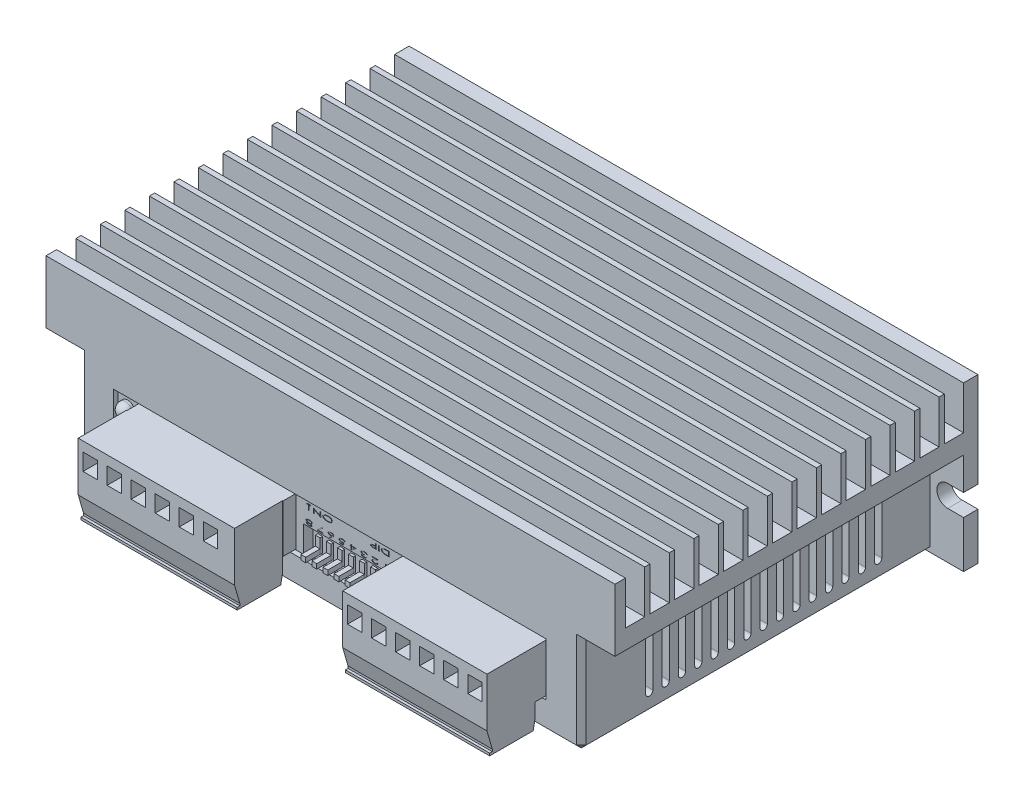
SolidWorks part; units mm, degrees
ref_plane "Ebene vorne" through (0, 0, 0) normal (0, 0, 1) x (1, 0, 0)
ref_plane "Ebene oben" through (0, 0, 0) normal (0, 1, 0) x (1, 0, 0)
ref_plane "Ebene rechts" through (0, 0, 0) normal (1, 0, 0) x (0, 0, -1)
sketch "Skizze1" plane through (0, 0, 0) normal (0, 0, 1) x (1, 0, 0)
  line L1 (-50.054, 15.2488) -> (68.246, 15.2488)
  line L2 (-50.054, 15.2488) -> (-50.054, -18.7512)
  line L3 (-50.054, -18.7512) -> (68.246, -18.7512)
  line L4 (68.246, 15.2488) -> (68.246, -18.7512)
  dimension "D1" = 118.3
  dimension "D2" = 34
extrude "Grundkörper" add sketch "Skizze1" along normal blind 75.5
sketch "Skizze2" plane through (0, 0, 75.5) normal (0, 0, 1) x (1, 0, 0)
  line L0 (-50.054, 15.2488) -> (-50.054, -18.7512) construction
  line L1 (-50.054, -18.7512) -> (68.246, -18.7512) construction
  line L2 (-47.054, -9.0012) -> (-50.054, -9.0012)
  line L3 (-50.054, -9.0012) -> (-50.054, -4.5012)
  line L4 (-50.054, -4.5012) -> (-47.054, -4.5012)
  line L5 (64.946, -4.5012) -> (68.246, -4.5012)
  line L6 (68.246, -4.5012) -> (68.246, -9.0012)
  line L7 (68.246, -9.0012) -> (64.946, -9.0012)
  arc A0 (-47.054, -9.0012) -> (-47.054, -4.5012) centre (-47.054, -6.7512) ccw
  arc A1 (64.946, -4.5012) -> (64.946, -9.0012) centre (64.946, -6.7512) ccw
  dimension "D2" = 4.5
  dimension "D3" = 112
  dimension "D4" = 3
  dimension "D5" = 12
  dimension "D6" = 12
  dimension "D8" = 2.25
extrude "Befestigung" cut sketch "Skizze2" against normal through all
sketch "Skizze3" plane through (0, 0, 75.5) normal (0, 0, 1) x (1, 0, 0)
  line L0 (68.246, -4.5012) -> (68.246, 15.2488) construction
  line L1 (-50.054, 2.2488) -> (-43.054, 2.2488)
  line L2 (-50.054, 2.2488) -> (-50.054, -18.7512)
  line L3 (-50.054, -18.7512) -> (-43.054, -18.7512)
  line L4 (-43.054, 2.2488) -> (-43.054, -18.7512)
  line L5 (68.246, 2.2488) -> (61.246, 2.2488)
  line L6 (68.246, 2.2488) -> (68.246, -18.7512)
  line L7 (68.246, -18.7512) -> (61.246, -18.7512)
  line L8 (61.246, 2.2488) -> (61.246, -18.7512)
  line L9 (-50.054, -18.7512) -> (68.246, -18.7512) construction
  dimension "D1" = 7
  dimension "D2" = 7
  dimension "D3" = 0
  dimension "D4" = 21
  dimension "D5" = 21
  dimension "D6" = 0
extrude "Seitentaschen" cut sketch "Skizze3" against normal blind 72.5
sketch "Skizze4" plane through (0, 15.2488, 0) normal (0, 1, 0) x (1, 0, 0)
  line L0 (68.246, 0) -> (-50.054, 0) construction
  line L1 (-50.054, -3) -> (68.246, -3)
  line L2 (-50.054, -3) -> (-50.054, -7)
  line L3 (-50.054, -7) -> (68.246, -7)
  line L4 (68.246, -3) -> (68.246, -7)
  dimension "D1" = 3
  dimension "D2" = 4
extrude "Kühlrippen hinten" cut sketch "Skizze4" against normal blind 9
pattern_linear "Kühlrippen hinten Muster" count 14 spacing 5.1 along (0, 0, 1) of "Kühlrippen hinten"
sketch "Skizze5" plane through (-43.054, 0, 0) normal (-1, 0, 0) x (0, 0, 1)
  line L0 (13.75, -4.7512) -> (13.75, -14.7512) construction
  line L1 (14.5, -4.7512) -> (14.5, -14.7512)
  line L2 (13, -4.7512) -> (13, -14.7512)
  line L3 (3, -9.0012) -> (3, -18.7512) construction
  line L4 (3, -18.7512) -> (75.5, -18.7512) construction
  arc A0 (14.5, -4.7512) -> (13, -4.7512) centre (13.75, -4.7512) ccw
  arc A1 (13, -14.7512) -> (14.5, -14.7512) centre (13.75, -14.7512) ccw
  point P2 (13.75, -9.7512)
  dimension "D3" = 10
  dimension "D1" = 1.5
  dimension "D2" = 10
  dimension "D4" = 4
extrude "Kühlrippen seite" cut sketch "Skizze5" against normal through all
pattern_linear "Kühlrippen seite muster" count 15 spacing 3.4 along (0, 0, 1) of "Kühlrippen seite"
sketch "Skizze6" plane through (0, 0, 75.5) normal (0, 0, 1) x (1, 0, 0)
  line L0 (-43.054, -18.7512) -> (-43.054, 2.2488) construction
  line L1 (-36.054, -12.7512) -> (53.946, -12.7512)
  line L2 (-36.054, -12.7512) -> (-36.054, -1.7512)
  line L3 (-36.054, -1.7512) -> (53.946, -1.7512)
  line L4 (53.946, -12.7512) -> (53.946, -1.7512)
  line L5 (68.246, 15.2488) -> (-50.054, 15.2488) construction
  dimension "D1" = 90
  dimension "D2" = 11
  dimension "D3" = 7
  dimension "D4" = 17
extrude "Tasche" cut sketch "Skizze6" against normal blind 1
sketch "Skizze7" plane through (0, 0, 74.5) normal (0, 0, 1) x (1, 0, 0)
  line L0 (53.946, -1.7512) -> (-36.054, -1.7512) construction
  line L1 (-36.054, -1.7512) -> (-36.054, -12.7512) construction
  circle A0 centre (-34.054, -4.7512) radius 1.5
  circle A1 centre (-34.054, -9.7512) radius 1.5
  dimension "D1" = 3
  dimension "D2" = 3
  dimension "D3" = 5
  dimension "D4" = 3
  dimension "D5" = 2
extrude "Leds" add sketch "Skizze7" along normal blind 2
fillet "Led Grün" radius 1.5 1 edges at (-32.554, -4.7512, 76.5)
fillet "Led Rot" radius 1.5 1 edges at (-32.554, -9.7512, 76.5)
sketch "Skizze8" plane through (0, 0, 74.5) normal (0, 0, 1) x (1, 0, 0)
  line L0 (-36.054, -12.7512) -> (53.946, -12.7512) construction
  line L1 (1.446, -2.2512) -> (23.446, -2.2512)
  line L2 (1.446, -2.2512) -> (1.446, -12.2512)
  line L3 (1.446, -12.2512) -> (23.446, -12.2512)
  line L4 (23.446, -2.2512) -> (23.446, -12.2512)
  dimension "D1" = 22
  dimension "D2" = 10
  dimension "D3" = 0.5
  dimension "D4" = 30.5
extrude "DIP Schalter Fläche" add sketch "Skizze8" along normal blind 0.5
sketch "Skizze9" plane through (0, 0, 75) normal (0, 0, 1) x (1, 0, 0)
  line L0 (23.446, -12.2512) -> (23.446, -2.2512) construction
  line L1 (2.946, -12.2512) -> (21.946, -12.2512)
  line L2 (2.946, -12.2512) -> (2.946, -6.7512)
  line L3 (2.946, -6.7512) -> (21.946, -6.7512)
  line L4 (21.946, -12.2512) -> (21.946, -6.7512)
  line L5 (1.446, -12.2512) -> (23.446, -12.2512) construction
  dimension "D1" = 19
  dimension "D2" = 1.5
  dimension "D3" = 5.5
  dimension "D4" = 0
extrude "DIP Schalter Vertiefung" cut sketch "Skizze9" against normal blind 2
sketch "Skizze10" plane through (0, 0, 73) normal (0, 0, 1) x (1, 0, 0)
  line L0 (2.946, -6.7512) -> (2.946, -12.2512) construction
  line L1 (3.946, -9.0512) -> (4.946, -9.0512)
  line L2 (3.946, -9.0512) -> (3.946, -12.0512)
  line L3 (3.946, -12.0512) -> (4.946, -12.0512)
  line L4 (4.946, -9.0512) -> (4.946, -12.0512)
  line L5 (2.946, -12.2512) -> (21.946, -12.2512) construction
  dimension "D1" = 1
  dimension "D2" = 3
  dimension "D3" = 1
  dimension "D4" = 0.2
extrude "DIP Schalter Schalter boden" add sketch "Skizze10" along normal blind 0.5
pattern_linear "DIP Schalter Schalter boden muster" count 8 spacing 2.3 along (1, 0, 0) of "DIP Schalter Schalter boden"
sketch "Skizze11" plane through (0, 0, 74.5) normal (0, 0, 1) x (1, 0, 0)
  line L1 (4.9426, -12.0512) -> (3.9426, -12.0512)
  line L2 (4.9426, -12.0512) -> (4.9426, -11.0512)
  line L3 (4.9426, -11.0512) -> (3.9426, -11.0512)
  line L4 (3.9426, -12.0512) -> (3.9426, -11.0512)
  dimension "D1" = 1
  dimension "D2" = 1
extrude "DIP Schalter Hebel" add sketch "Skizze11" along normal blind 3 from offset 1 separate body offset against normal yes
pattern_linear "DIP Schalter Hebel Muster" count 8 spacing 2.3 along (1, 0, 0) of "DIP Schalter Hebel"
sketch "Skizze12" plane through (0, 0, 75) normal (0, 0, 1) x (1, 0, 0)
  line L0 (3.4242, -5.4773) -> (23.446, -5.4773) construction
  text T0 "1 2 3 4 5 6 7 8\r\nDIP          ON↓" font "Century Gothic" height 1
extrude "DIP Schalter Schrift" cut sketch "Skizze12" against normal blind 0.1
sketch "Skizze14" plane through (0, 0, 74.5) normal (0, 0, 1) x (1, 0, 0)
  line L0 (23.446, -12.2512) -> (23.446, -2.2512) construction
  line L1 (23.646, -2.2512) -> (53.646, -2.2512)
  line L2 (23.646, -2.2512) -> (23.646, -12.2512)
  line L3 (23.646, -12.2512) -> (53.646, -12.2512)
  line L4 (53.646, -2.2512) -> (53.646, -12.2512)
  line L5 (-36.054, -12.7512) -> (53.946, -12.7512) construction
  line L6 (53.946, -1.7512) -> (-36.054, -1.7512) construction
  line L7 (1.246, -2.2512) -> (-31.254, -2.2512)
  line L8 (1.246, -2.2512) -> (1.246, -12.2512)
  line L9 (1.246, -12.2512) -> (-31.254, -12.2512)
  line L10 (-31.254, -2.2512) -> (-31.254, -12.2512)
  line L11 (1.446, -2.2512) -> (1.446, -12.2512) construction
  dimension "D1" = 30
  dimension "D2" = 0.2
  dimension "D3" = 10
  dimension "D4" = 0.5
  dimension "D5" = 32.5
  dimension "D6" = 10
  dimension "D7" = 0.5
  dimension "D8" = 0.2
extrude "Anschlüsse Grund" add sketch "Skizze14" along normal blind 3
sketch "Skizze15" plane through (0, 0, 77.5) normal (0, 0, 1) x (1, 0, 0)
  line L0 (1.246, -2.2512) -> (-31.254, -2.2512) construction
  line L1 (53.646, -2.2512) -> (23.646, -2.2512)
  line L2 (53.646, -2.2512) -> (53.646, -17.2512)
  line L3 (53.646, -17.2512) -> (23.646, -17.2512)
  line L4 (23.646, -2.2512) -> (23.646, -17.2512)
  line L5 (1.1491, -2.2512) -> (-31.3509, -2.2512)
  line L6 (1.1491, -2.2512) -> (1.1491, -17.2512)
  line L7 (1.1491, -17.2512) -> (-31.3509, -17.2512)
  line L8 (-31.3509, -2.2512) -> (-31.3509, -17.2512)
  line L9 (53.646, -2.2512) -> (23.646, -2.2512) construction
  dimension "D1" = 32.5
  dimension "D2" = 30
  dimension "D3" = 15
  dimension "D4" = 0
  dimension "D5" = 15
  dimension "D6" = 0
extrude "Anschlüsse Block" add sketch "Skizze15" along normal blind 10
sketch "Skizze17" plane through (-31.3509, 0, 0) normal (-1, 0, 0) x (0, 0, 1)
  line L0 (87.5, -12.4761) -> (86.3973, -16.3153)
  line L1 (86.3973, -16.3153) -> (86.3973, -16.7527)
  line L2 (86.3973, -16.7527) -> (86.9486, -16.7527)
  line L3 (86.9486, -16.7527) -> (86.9486, -17.2512)
  line L4 (86.9486, -17.2512) -> (87.5, -17.2512)
  line L5 (87.5, -17.2512) -> (87.5, -12.4761)
  line L6 (77.5, -15.2462) -> (77.8927, -17.2512)
  line L7 (77.8927, -17.2512) -> (77.5, -17.2512)
  line L8 (77.5, -17.2512) -> (77.5, -15.2462)
extrude "Anschluss Profil" cut sketch "Skizze17" against normal through all
sketch "Skizze18" plane through (0, 0, 87.5) normal (0, 0, 1) x (1, 0, 0)
  line L1 (-30.3509, -4.2512) -> (-27.3509, -4.2512)
  line L2 (-30.3509, -4.2512) -> (-30.3509, -7.7512)
  line L3 (-30.3509, -7.7512) -> (-27.3509, -7.7512)
  line L4 (-27.3509, -4.2512) -> (-27.3509, -7.7512)
  line L5 (-31.3509, -2.2512) -> (-31.3509, -12.4761) construction
  line L6 (1.246, -2.2512) -> (-31.254, -2.2512) construction
  line L7 (23.646, -2.2512) -> (23.646, -12.4761) construction
  line L8 (24.646, -4.2512) -> (27.646, -4.2512)
  line L9 (24.646, -4.2512) -> (24.646, -7.7512)
  line L10 (24.646, -7.7512) -> (27.646, -7.7512)
  line L11 (27.646, -4.2512) -> (27.646, -7.7512)
  line L12 (53.646, -2.2512) -> (23.646, -2.2512) construction
  dimension "D1" = 3
  dimension "D2" = 3.5
  dimension "D3" = 1
  dimension "D4" = 2
  dimension "D5" = 3
  dimension "D6" = 3.5
  dimension "D7" = 1
  dimension "D8" = 2
extrude "Anschluss Kabel" cut sketch "Skizze18" against normal blind 5
pattern_linear "Anschluss Kabel Muster" count 6 spacing 5 along (1, 0, 0) of "Anschluss Kabel"
sketch "Skizze19" plane through (0, -17.2512, 0) normal (0, -1, 0) x (1, 0, 0)
  line L0 (1.1491, 77.8927) -> (-31.3509, 77.8927) construction
  line L1 (53.646, 77.8927) -> (23.646, 77.8927) construction
  line L2 (-31.3509, 86.9486) -> (-31.3509, 77.8927) construction
  line L3 (23.646, 86.9486) -> (23.646, 77.8927) construction
  line L4 (-31.3509, 87.5) -> (1.1491, 87.5) construction
  line L5 (-29.6009, 86) -> (-28.1009, 86)
  line L6 (-29.6009, 86) -> (-29.6009, 85)
  line L7 (-29.6009, 85) -> (-28.1009, 85)
  line L8 (-28.1009, 86) -> (-28.1009, 85)
  line L9 (25.396, 86) -> (26.896, 86)
  line L10 (25.396, 86) -> (25.396, 85)
  line L11 (25.396, 85) -> (26.896, 85)
  line L12 (26.896, 86) -> (26.896, 85)
  line L13 (53.646, 87.5) -> (23.646, 87.5) construction
  circle A0 centre (-28.8509, 80.8927) radius 1.8
  circle A1 centre (26.146, 80.8927) radius 1.8
  point P12 (23.646, 82.4207)
  dimension "D1" = 3.6
  dimension "D2" = 3.6
  dimension "D3" = 3
  dimension "D4" = 3
  dimension "D5" = 2.5
  dimension "D6" = 2.5
  dimension "D7" = 1.5
  dimension "D8" = 1
  dimension "D9" = 1.5
  dimension "D10" = 1.75
  dimension "D11" = 1.5
  dimension "D12" = 1.75
  dimension "D13" = 1.5
  dimension "D14" = 1
extrude "Schrauben Löcher" cut sketch "Skizze19" against normal blind 2
pattern_linear "Schrauben Löcher Muster" count 6 spacing 5 along (1, 0, 0) of "Schrauben Löcher"
sketch "Skizze22" plane through (0, -15.2512, 0) normal (0, -1, 0) x (1, 0, 0)
  circle A0 centre (-28.8509, 80.8927) radius 1.6499
  circle A1 centre (26.146, 80.8927) radius 1.6477
extrude "Schraube Körper" add sketch "Skizze22" along normal blind 1
pattern_linear "Schraube Körper Muster" count 6 spacing 5 along (1, 0, 0) of "Schraube Körper"
sketch "Skizze23" plane through (0, -16.2512, 0) normal (0, -1, 0) x (1, 0, 0)
  line L0 (-29.3769, 82.4469) -> (-29.3769, 81.377)
  line L1 (-29.3769, 81.377) -> (-30.4469, 81.377)
  line L2 (-30.4469, 81.377) -> (-30.4469, 80.377)
  line L3 (-30.4469, 80.377) -> (-29.3769, 80.377)
  line L4 (-29.3769, 80.377) -> (-29.3769, 79.307)
  line L5 (-29.3769, 79.307) -> (-28.3769, 79.307)
  line L6 (-28.3769, 79.307) -> (-28.3769, 80.377)
  line L7 (-28.3769, 80.377) -> (-27.307, 80.377)
  line L8 (-27.307, 80.377) -> (-27.307, 81.377)
  line L9 (-27.307, 81.377) -> (-28.3769, 81.377)
  line L10 (-28.3769, 81.377) -> (-28.3769, 82.4469)
  line L11 (-28.3769, 82.4469) -> (-29.3769, 82.4469)
  line L12 (25.6092, 82.415) -> (25.6092, 81.377)
  line L13 (25.6092, 81.377) -> (24.5711, 81.377)
  line L14 (24.5711, 81.377) -> (24.5711, 80.3769)
  line L15 (24.5711, 80.3769) -> (25.6092, 80.3769)
  line L16 (25.6092, 80.3769) -> (25.6092, 79.3389)
  line L17 (25.6092, 79.3389) -> (26.6092, 79.3389)
  line L18 (26.6092, 79.3389) -> (26.6092, 80.3769)
  line L19 (26.6092, 80.3769) -> (27.6472, 80.3769)
  line L20 (27.6472, 80.3769) -> (27.6472, 81.377)
  line L21 (27.6472, 81.377) -> (26.6092, 81.377)
  line L22 (26.6092, 81.377) -> (26.6092, 82.415)
  line L23 (26.6092, 82.415) -> (25.6092, 82.415)
  dimension "D1" = 1
  dimension "D7" = 1
  dimension "D8" = 1.0001
  dimension "D9" = 1
extrude "Schraube Kreuz" cut sketch "Skizze23" along direction (0, -1, 0) on the side against the normal blind 0.2 draft 1 from offset 0
pattern_linear "Schraube Kreuz Muster" count 6 spacing 5 along (1, 0, 0) of "Schraube Kreuz"
chamfer "Fase1" distance 1 angle 45 5 edges at (61.246, -8.2512, 75.5) (61.246, -18.7512, 39.25) (-43.054, -18.7512, 39.25) (9.096, -18.7512, 75.5) (-43.054, -8.2512, 75.5)
